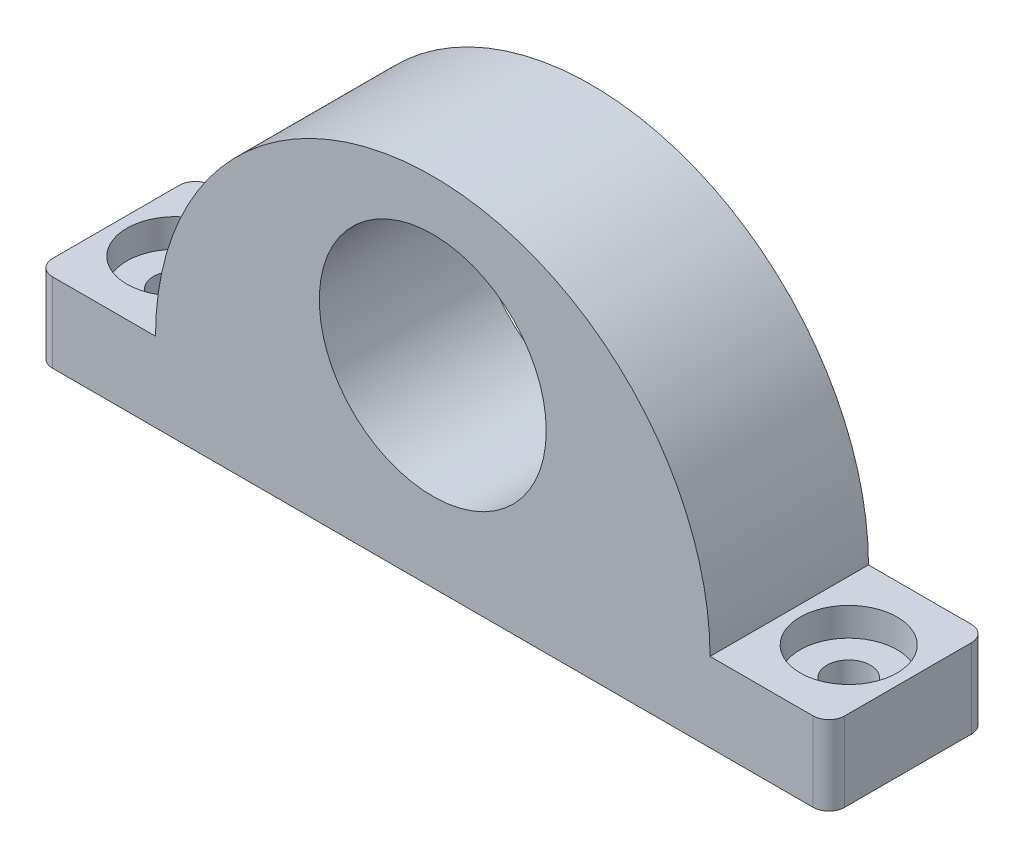
SolidWorks part; units mm, degrees
ref_plane "Front Plane" through (0, 0, 0) normal (0, 0, 1) x (1, 0, 0)
ref_plane "Top Plane" through (0, 0, 0) normal (0, 1, 0) x (1, 0, 0)
ref_plane "Right Plane" through (0, 0, 0) normal (1, 0, 0) x (0, 0, -1)
sketch "Sketch3" plane through (0, 0, 0) normal (0, 0, 1) x (1, 0, 0)
  line L0 (0, 19.325) -> (0, 0) construction
  line L2 (-35, 5) -> (-35, -5)
  line L3 (-35, -5) -> (35, -5)
  line L4 (35, 5) -> (35, -5)
  line L5 (35, 5) -> (50, 5)
  line L6 (-35, -5) -> (-50, -5)
  line L7 (-35, -5) -> (-35, 5)
  line L8 (-35, 5) -> (-50, 5)
  line L9 (-50, -5) -> (-50, 5)
  line L10 (50, -5) -> (50, 5)
  line L11 (35, -5) -> (50, -5)
  line L12 (35, -5) -> (35, 5)
  circle A1 centre (0, 19.325) radius 14.325
  arc A3 (35, 5) -> (-35, 5) centre (0, 5) ccw
  point P0 (0, 0)
  dimension "D3" = 28.65
  dimension "D1" = 70
  dimension "D2" = 10
  dimension "D5" = 5
  dimension "D6" = 15
extrude "Boss-Extrude3" add sketch "Sketch3" along normal blind 20
hole_wizard "CBORE for M5 Hex Head Bolt1" positions "Sketch4" profile "Sketch5" counterbore size "M5" standard "ANSI Metric" end condition up to next
sketch "Sketch4" plane through (0, 5, 0) normal (0, 1, 0) x (1, 0, 0)
  line L0 (-35, 0) -> (-50, 0) construction
  line L1 (-50, -20) -> (-50, 0) construction
  line L2 (50, -20) -> (50, 0) construction
  line L3 (35, -20) -> (50, -20) construction
  point P0 (-42.5, -10)
  point P2 (42.5, -10)
  point P15 (44.9085, -6.9923)
  point P16 (0, 0)
  dimension "D1" = 10
  dimension "D2" = 7.5
  dimension "D3" = 7.5
  dimension "D4" = 10
sketch "Sketch5" plane through (-42.5, 5, 10) normal (1, 0, 0) x (0, 0, 1)
  line L0 (0, 0) -> (0, 10)
  line L1 (0, 10) -> (2.75, 10)
  line L3 (2.75, 10) -> (2.75, 3.58)
  line L4 (2.75, 3.58) -> (6.12, 3.58)
  line L5 (6.12, 3.58) -> (6.12, 0)
  line L7 (6.12, 0) -> (0, 0)
  line L11 (0, -6.35) -> (0, 107.95) construction
  dimension "Thru Hole Dia." = 5.5
  dimension "Thru Hole Depth" = 10
  dimension "C'Bore Dia." = 12.24
  dimension "C'Bore Depth" = 3.58
fillet "Fillet1" radius 2 4 edges at (-50, 0, 0) (50, 0, 0) (50, 0, 20) (-50, 0, 20)
